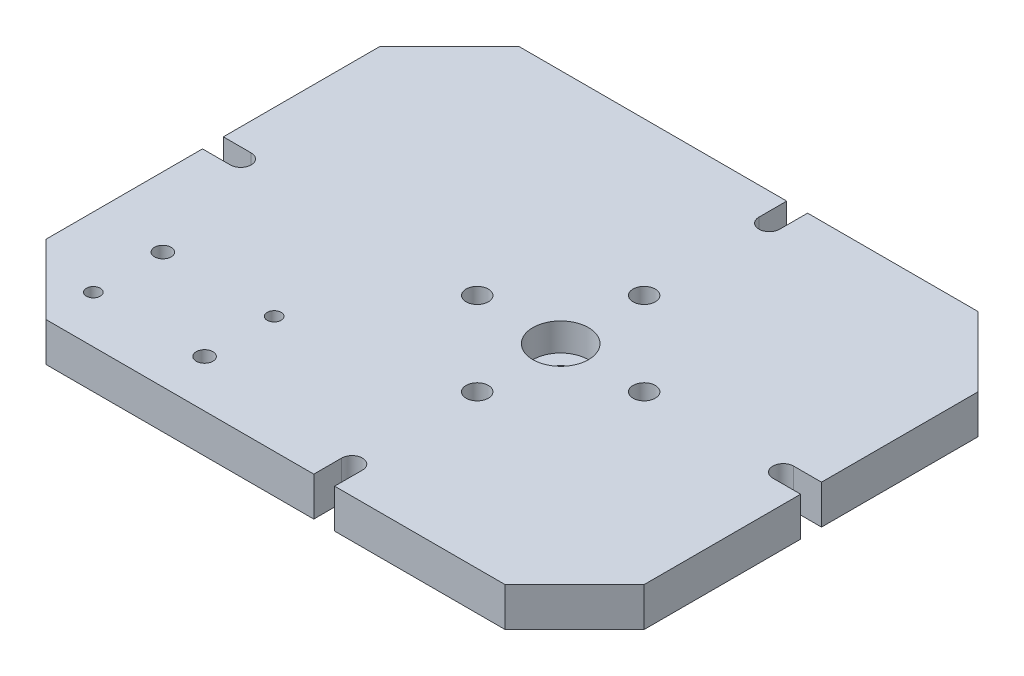
SolidWorks part; units mm, degrees
ref_plane "Спереди" through (0, 0, 0) normal (0, 0, 1) x (1, 0, 0)
ref_plane "Сверху" through (0, 0, 0) normal (0, 1, 0) x (1, 0, 0)
ref_plane "Справа" through (0, 0, 0) normal (1, 0, 0) x (0, 0, -1)
sketch "Эскиз1" plane through (0, 0, 0) normal (0, 1, 0) x (1, 0, 0)
  line L0 (0, 50) -> (50, 0)
  line L1 (50, 0) -> (242.5, 0)
  line L2 (0, 50) -> (0, 162.5)
  line L3 (50, 340) -> (242.5, 340)
  line L4 (430, 50) -> (430, 162.5)
  line L5 (0, 290) -> (50, 340)
  line L6 (430, 290) -> (380, 340)
  line L7 (380, 0) -> (430, 50)
  line L8 (-47.6005, 170) -> (493.9282, 170) construction
  line L9 (250, 367.0511) -> (250, -36.8008) construction
  line L10 (0, 177.5) -> (20, 177.5)
  line L11 (20, 162.5) -> (0, 162.5)
  line L12 (0, 177.5) -> (0, 290)
  line L13 (242.5, 320) -> (242.5, 340)
  line L14 (257.5, 340) -> (257.5, 320)
  line L15 (215, 350.5536) -> (215, 132.7263) construction
  line L16 (430, 177.5) -> (410, 177.5)
  line L17 (410, 162.5) -> (430, 162.5)
  line L18 (242.5, 20) -> (242.5, 0)
  line L19 (430, 177.5) -> (430, 290)
  line L20 (257.5, 340) -> (380, 340)
  line L21 (257.5, 0) -> (257.5, 20)
  line L22 (257.5, 0) -> (380, 0)
  arc A0 (20, 162.5) -> (20, 177.5) centre (20, 170) ccw
  arc A1 (242.5, 320) -> (257.5, 320) centre (250, 320) ccw
  arc A2 (410, 162.5) -> (410, 177.5) centre (410, 170) cw
  arc A3 (257.5, 20) -> (242.5, 20) centre (250, 20) ccw
  point P0 (0, 0)
  point P1 (430, 340)
  point P2 (0, 340)
  point P3 (430, 0)
  point P22 (27.5, 170)
  point P28 (250, 312.5)
  point P41 (250, 27.5)
  dimension "D5" = 7.5
  dimension "D6" = 27.5
  dimension "D7" = 7.5
  dimension "D13" = 7.5
  dimension "D1" = 340
  dimension "D2" = 430
  dimension "D3" = 250
  dimension "D4" = 170
  dimension "D8" = 27.5
  dimension "D14" = 27.5
extrude "Бобышка-Вытянуть1" add sketch "Эскиз1" along normal blind 28
sketch "Эскиз2" plane through (0, 28, 0) normal (0, 1, 0) x (1, 0, 0)
  line L0 (250, 351.1025) -> (250, -15.6801) construction
  line L1 (0, 162.5) -> (0, 50) construction
  line L2 (-16.1703, 170) -> (483.9358, 170) construction
  line L3 (50, 0) -> (242.5, 0) construction
  circle A0 centre (250, 170) radius 60 construction
  circle A1 centre (250, 230) radius 8
  circle A2 centre (190, 170) radius 8
  circle A3 centre (250, 110) radius 8
  circle A4 centre (310, 170) radius 8
  point P23 (250, 170)
  dimension "D3" = 120
  dimension "D4" = 16
  dimension "D1" = 250
  dimension "D2" = 170
extrude "Вырез-Вытянуть1" cut sketch "Эскиз2" against normal blind 28
sketch "Эскиз3" plane through (0, 28, 0) normal (0, 1, 0) x (1, 0, 0)
  line L0 (-13.4047, 170) -> (466.7696, 170) construction
  line L1 (250, -11.4363) -> (250, 42.4463) construction
  line L2 (50, 84) -> (130, 84) construction
  line L3 (50, 84) -> (50, 34) construction
  line L4 (50, 34) -> (130, 34) construction
  line L5 (130, 84) -> (130, 34) construction
  circle A0 centre (50, 84) radius 6
  circle A1 centre (130, 84) radius 5
  circle A2 centre (50, 34) radius 5
  circle A3 centre (130, 34) radius 6
  dimension "D5" = 12
  dimension "D6" = 12
  dimension "D7" = 10
  dimension "D8" = 10
  dimension "D1" = 86
  dimension "D2" = 50
  dimension "D3" = 80
  dimension "D4" = 120
extrude "Вырез-Вытянуть2" cut sketch "Эскиз3" against normal blind 28
sketch "Эскиз4" plane through (0, 28, 0) normal (0, 1, 0) x (1, 0, 0)
  circle A0 centre (250, 170) radius 20
  dimension "D1" = 40
extrude "Вырез-Вытянуть3" cut sketch "Эскиз4" against normal blind 20
sketch "Эскиз5" plane through (0, 8, 0) normal (0, 1, 0) x (1, 0, 0)
  circle A0 centre (250, 170) radius 9
  dimension "D1" = 18
extrude "Вырез-Вытянуть4" cut sketch "Эскиз5" against normal blind 20
